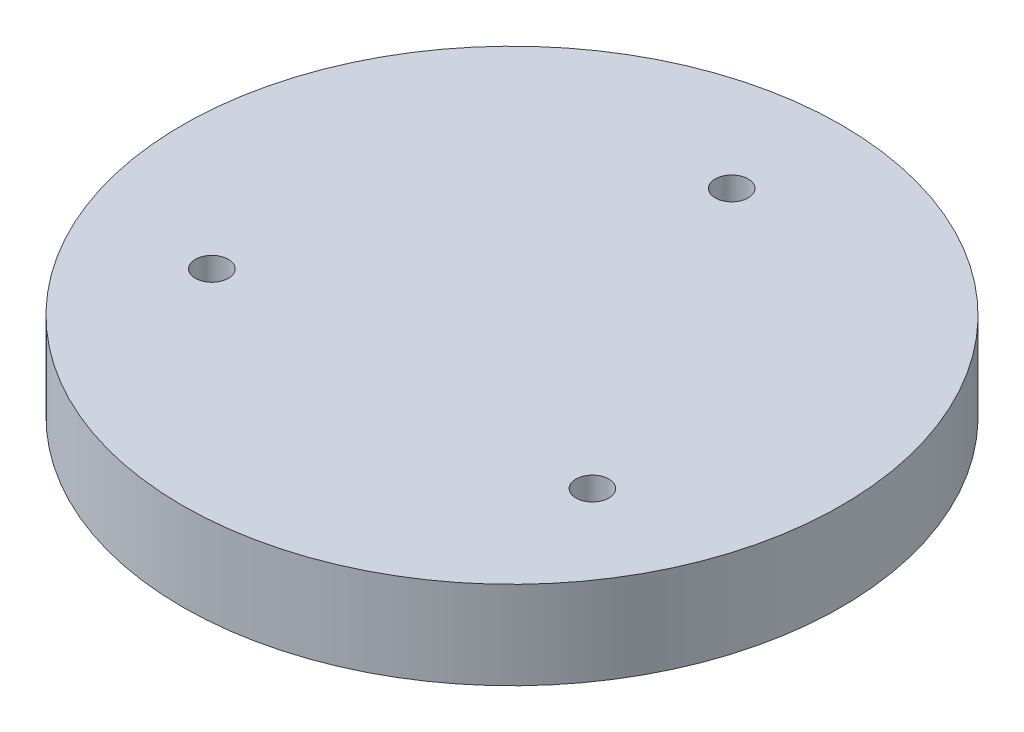
SolidWorks part; units mm, degrees
ref_plane "前视基准面" through (0, 0, 0) normal (0, 0, 1) x (1, 0, 0)
ref_plane "上视基准面" through (0, 0, 0) normal (0, 1, 0) x (1, 0, 0)
ref_plane "右视基准面" through (0, 0, 0) normal (1, 0, 0) x (0, 0, -1)
sketch "草图1" plane through (0, 0, 0) normal (0, 1, 0) x (1, 0, 0)
  circle A0 centre (0, 0) radius 30
extrude "凸台-拉伸1" add sketch "草图1" along normal blind 8
sketch "草图2" plane through (0, 8, 0) normal (0, 1, 0) x (1, 0, 0)
  circle A0 centre (0, 0) radius 20
  circle A1 centre (0, 20) radius 1.5
  circle A2 centre (17.3205, -10) radius 1.5
  circle A3 centre (-17.3205, -10) radius 1.5
  point P11 (0, 0)
  dimension "D1" = 3
extrude "切除-拉伸1" cut sketch "草图2" against normal blind 8 contours A1 | A3 | A2
